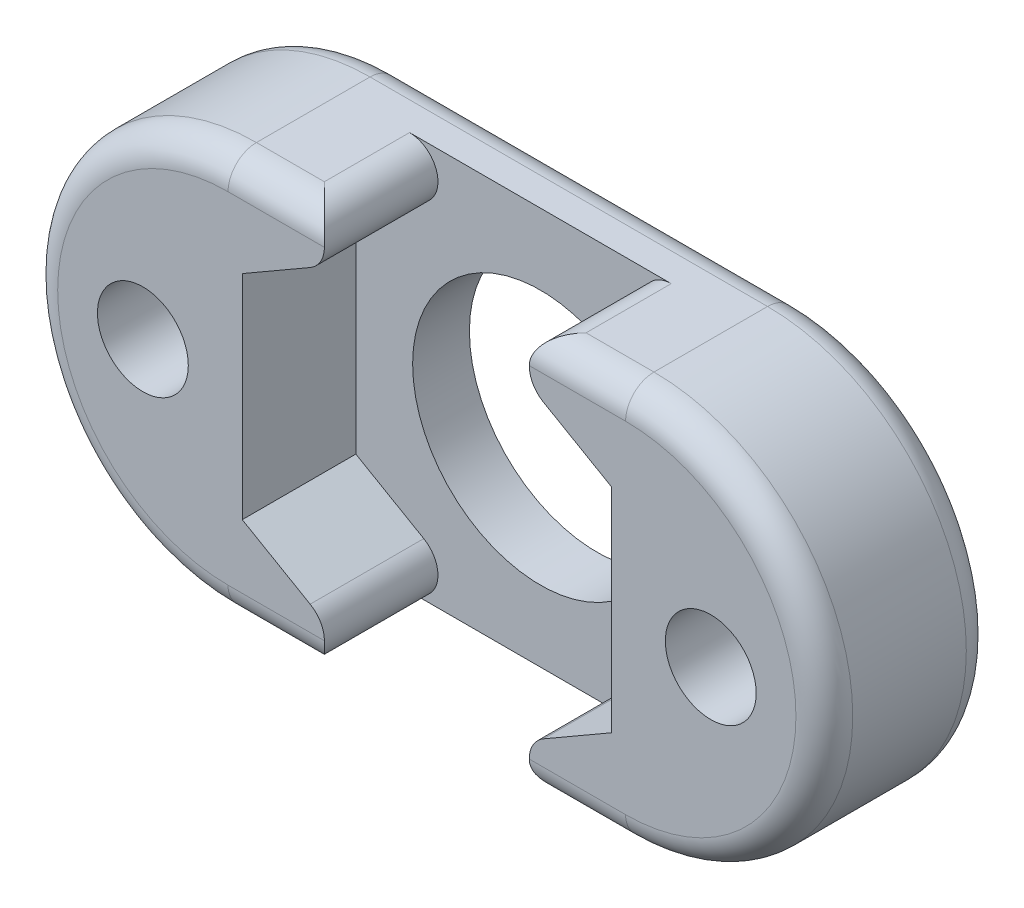
SolidWorks part; units mm, degrees
ref_plane "Plan de face" through (0, 0, 0) normal (0, 0, 1) x (1, 0, 0)
ref_plane "Plan de dessus" through (0, 0, 0) normal (0, 1, 0) x (1, 0, 0)
ref_plane "Plan de droite" through (0, 0, 0) normal (1, 0, 0) x (0, 0, -1)
sketch "Esquisse1" plane through (0, 0, 0) normal (0, 0, 1) x (1, 0, 0)
  line L0 (-27.2542, 0) -> (-13.2542, 0) construction
  line L1 (-27.2542, 7) -> (-13.2542, 7)
  line L2 (-27.2542, -7) -> (-13.2542, -7)
  arc A0 (-27.2542, 7) -> (-27.2542, -7) centre (-27.2542, 0) ccw
  arc A1 (-13.2542, -7) -> (-13.2542, 7) centre (-13.2542, 0) ccw
  point P3 (-20.2542, 0)
  dimension "D1" = 14
  dimension "D2" = 14
extrude "Boss.-Extru.1" add sketch "Esquisse1" along normal blind 6
sketch "Esquisse3" plane through (0, 0, 6) normal (0, 0, 1) x (1, 0, 0)
  line L0 (-27.2542, -7) -> (-13.2542, -7) construction
  circle A0 centre (-20.2542, 0) radius 4.5
  circle A1 centre (-30.2542, 0) radius 1.6
  circle A2 centre (-10.2542, 0) radius 1.6
  dimension "D1" = 3.2
  dimension "D2" = 3.2
  dimension "D5" = 9
  dimension "D3" = 20
  dimension "D4" = 10
  dimension "D6" = 7
  dimension "D7" = 7
  dimension "D8" = 7
  dimension "D9" = 7
extrude "Enlèv. mat.-Extru.1" cut sketch "Esquisse3" against normal through all
sketch "Esquisse4" plane through (0, 0, 6) normal (0, 0, 1) x (1, 0, 0)
  line L8 (-13.7542, -3.7528) -> (-13.7542, 3.7528)
  line L9 (-13.7542, 3.7528) -> (-20.2542, 7.5056)
  line L10 (-20.2542, 7.5056) -> (-26.7542, 3.7528)
  line L11 (-26.7542, 3.7528) -> (-26.7542, -3.7528)
  line L12 (-26.7542, -3.7528) -> (-20.2542, -7.5056)
  line L13 (-20.2542, -7.5056) -> (-13.7542, -3.7528)
  circle A1 centre (-20.2542, 0) radius 6.5 construction
  dimension "D2" = 13
extrude "Enlèv. mat.-Extru.2" cut sketch "Esquisse4" against normal blind 4
fillet "Congé1" radius 1 14 edges at (-24.192, 7, 6) (-16.3164, 7, 6) (-6.2542, 0, 6) (-16.3164, -7, 6) (-24.192, -7, 6) (-20.2542, 7, 0) (-6.2542, 0, 0) (-20.2542, -7, 0) (-34.2542, 0, 6) (-34.2542, 0, 0) (-19.3785, 7, 4) (-21.1298, 7, 4) (-19.3785, -7, 4) (-21.1298, -7, 4)
